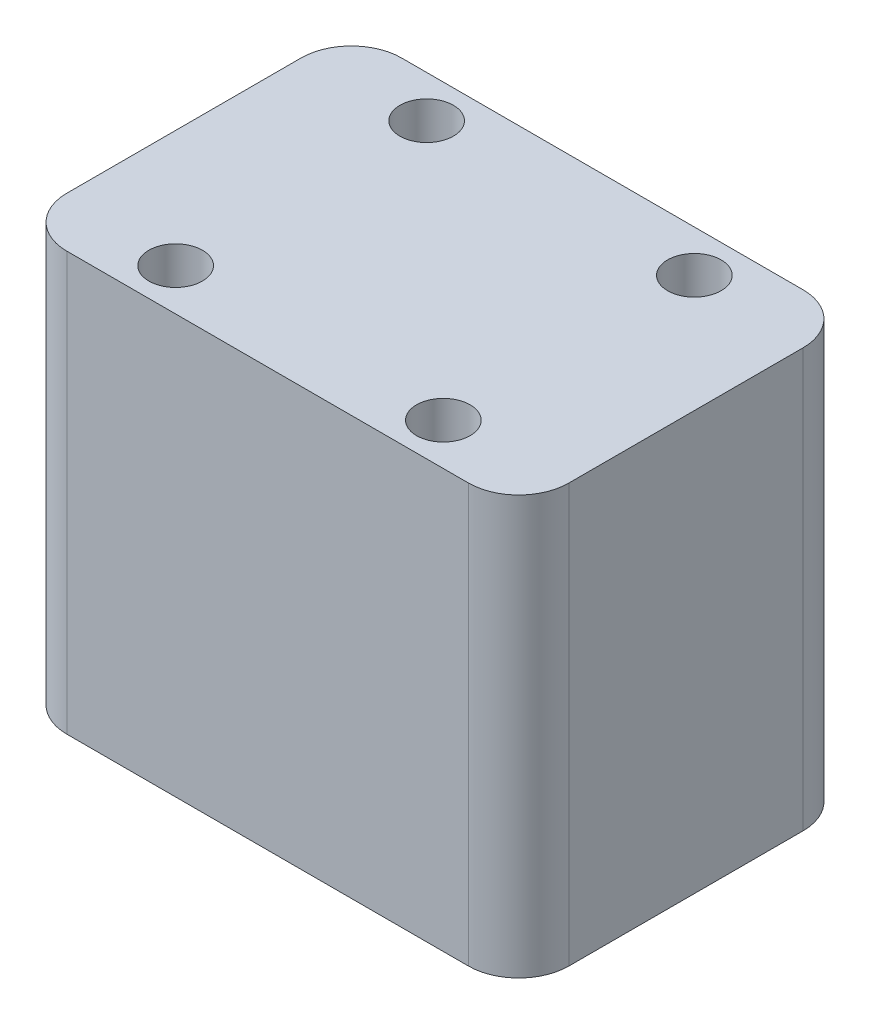
SolidWorks part; units mm, degrees
ref_plane "前视基准面" through (0, 0, 0) normal (0, 0, 1) x (1, 0, 0)
ref_plane "上视基准面" through (0, 0, 0) normal (0, 1, 0) x (1, 0, 0)
ref_plane "右视基准面" through (0, 0, 0) normal (1, 0, 0) x (0, 0, -1)
sketch "草图1" plane through (0, 0, 0) normal (0, 1, 0) x (1, 0, 0)
  line L1 (-15, 10) -> (15, 10)
  line L2 (-15, 10) -> (-15, -10)
  line L3 (-15, -10) -> (15, -10)
  line L4 (15, 10) -> (15, -10)
  line L5 (-15, 10) -> (15, -10) construction
  line L6 (-15, -10) -> (15, 10) construction
  line L7 (-8, 7.5) -> (8, 7.5) construction
  line L8 (-8, 7.5) -> (-8, -7.5) construction
  line L9 (-8, -7.5) -> (8, -7.5) construction
  line L10 (8, 7.5) -> (8, -7.5) construction
  line L11 (-8, 7.5) -> (8, -7.5) construction
  line L12 (-8, -7.5) -> (8, 7.5) construction
  circle A0 centre (-8, 7.5) radius 1.6
  circle A1 centre (-8, -7.5) radius 1.6
  circle A2 centre (8, -7.5) radius 1.6
  circle A3 centre (8, 7.5) radius 1.6
  point P0 (0, 0)
  point P5 (0, 0)
  dimension "D1" = 3.2
  dimension "D2" = 20
  dimension "D3" = 30
  dimension "D4" = 16
  dimension "D5" = 15
extrude "凸台-拉伸1" add sketch "草图1" along normal blind 25
fillet "圆角1" radius 3 4 edges at (15, 12.5, -10) (-15, 12.5, -10) (-15, 12.5, 10) (15, 12.5, 10)
